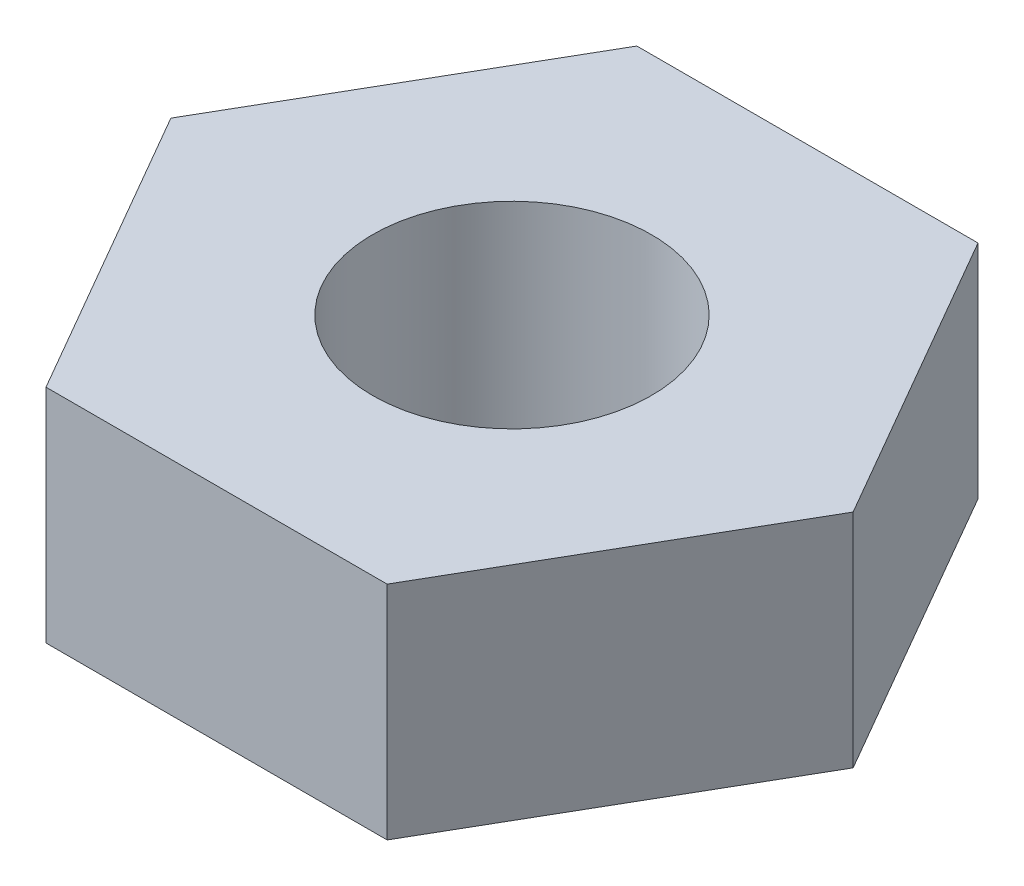
SolidWorks part; units mm, degrees
ref_plane "Front Plane" through (0, 0, 0) normal (0, 0, 1) x (1, 0, 0)
ref_plane "Top Plane" through (0, 0, 0) normal (0, 1, 0) x (1, 0, 0)
ref_plane "Right Plane" through (0, 0, 0) normal (1, 0, 0) x (0, 0, -1)
sketch "Sketch1" plane through (0, 0, 0) normal (0, 1, 0) x (1, 0, 0)
  line L1 (1.8331, 3.175) -> (-1.8331, 3.175)
  line L2 (-1.8331, 3.175) -> (-3.6662, 0)
  line L3 (-3.6662, 0) -> (-1.8331, -3.175)
  line L4 (-1.8331, -3.175) -> (1.8331, -3.175)
  line L5 (1.8331, -3.175) -> (3.6662, 0)
  line L6 (3.6662, 0) -> (1.8331, 3.175)
  circle A0 centre (0, 0) radius 3.175 construction
  circle A1 centre (0, 0) radius 1.4986
  dimension "D2" = 2.9972
  dimension "D1" = 6.35
extrude "Boss-Extrude1" add sketch "Sketch1" along normal blind 2.3813
